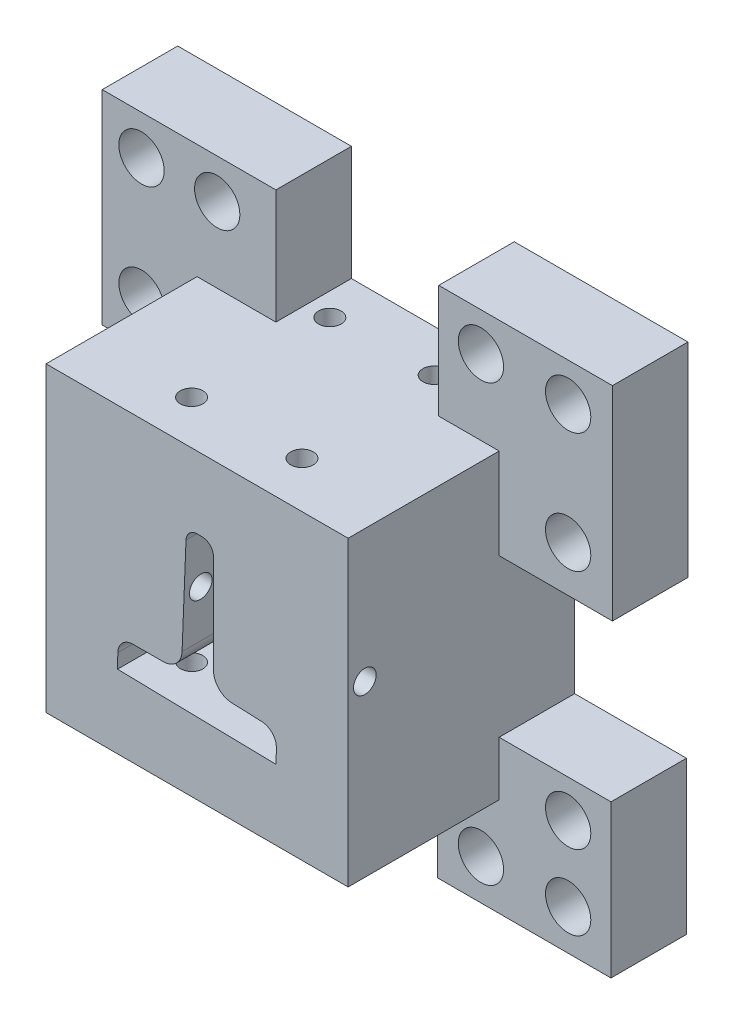
SolidWorks part; units mm, degrees
ref_plane "Plan de face" through (0, 0, 0) normal (0, 0, 1) x (1, 0, 0)
ref_plane "Plan de dessus" through (0, 0, 0) normal (0, 1, 0) x (1, 0, 0)
ref_plane "Plan de droite" through (0, 0, 0) normal (1, 0, 0) x (0, 0, -1)
sketch "Esquisse1" plane through (0, 0, 0) normal (0, 0, 1) x (1, 0, 0)
  line L0 (0, 699.6358) -> (0, -119.0526) construction
  line L1 (-20, 579.5765) -> (20, 579.5765)
  line L2 (-20, 579.5765) -> (-20, 539.5765)
  line L3 (-20, 539.5765) -> (20, 539.5765)
  line L4 (20, 579.5765) -> (20, 539.5765)
  line L5 (-10.0257, 549.7771) -> (9.9703, 549.3771) construction
  line L6 (9.9703, 549.3771) -> (9.9989, 550.8065) construction
  line L7 (8.5592, 552.3353) -> (4.552, 552.4957) construction
  line L8 (1.672, 555.4933) -> (1.672, 568.5669) construction
  line L9 (-0.9666, 568.6197) -> (-1.4895, 555.5565) construction
  line L10 (-4.4871, 552.6765) -> (-8.4974, 552.6765) construction
  line L11 (-10.0257, 549.7771) -> (-9.9971, 551.2065) construction
  line L12 (0.0526, 569.5795) -> (0.692, 569.5667) construction
  line L13 (-10.0257, 549.7771) -> (9.9703, 549.3771)
  line L14 (9.9703, 549.3771) -> (9.9989, 550.8065)
  line L15 (8.5592, 552.3353) -> (4.552, 552.4957)
  line L16 (1.672, 555.4933) -> (1.672, 568.5669)
  line L17 (-0.9666, 568.6197) -> (-1.4895, 555.5565)
  line L18 (-4.4871, 552.6765) -> (-8.4974, 552.6765)
  line L19 (-10.0257, 549.7771) -> (-9.9971, 551.2065)
  line L20 (0.0526, 569.5795) -> (0.692, 569.5667)
  arc A0 (9.9989, 550.8065) -> (8.5592, 552.3353) centre (8.4992, 550.8365) ccw construction
  arc A1 (1.672, 555.4933) -> (4.552, 552.4957) centre (4.672, 555.4933) ccw construction
  arc A2 (1.672, 568.5669) -> (0.692, 569.5667) centre (0.672, 568.5669) ccw construction
  arc A3 (0.0526, 569.5795) -> (-0.9666, 568.6197) centre (0.0326, 568.5797) ccw construction
  arc A4 (-4.4871, 552.6765) -> (-1.4895, 555.5565) centre (-4.4871, 555.6765) ccw construction
  arc A5 (-8.4974, 552.6765) -> (-9.9971, 551.2065) centre (-8.4974, 551.1765) ccw construction
  arc A6 (9.9989, 550.8065) -> (8.5592, 552.3353) centre (8.4992, 550.8365) ccw
  arc A7 (1.672, 555.4933) -> (4.552, 552.4957) centre (4.672, 555.4933) ccw
  arc A8 (1.672, 568.5669) -> (0.692, 569.5667) centre (0.672, 568.5669) ccw
  arc A9 (0.0526, 569.5795) -> (-0.9666, 568.6197) centre (0.0326, 568.5797) ccw
  arc A10 (-4.4871, 552.6765) -> (-1.4895, 555.5565) centre (-4.4871, 555.6765) ccw
  arc A11 (-8.4974, 552.6765) -> (-9.9971, 551.2065) centre (-8.4974, 551.1765) ccw
  dimension "D1" = 20
  dimension "D2" = 20
  dimension "D3" = 40
extrude "Boss.-Extru.1" add sketch "Esquisse1" along normal blind 30
sketch "Esquisse3" plane through (0, 0, 30) normal (0, 0, 1) x (1, 0, 0)
  line L16 (0.702, 570.0666) -> (0.0626, 570.0794)
  line L17 (-1.4662, 568.6397) -> (-1.9891, 555.5765)
  line L18 (-4.4871, 553.1765) -> (-8.4974, 553.1765)
  line L19 (-10.497, 551.2165) -> (-10.5356, 549.2872)
  line L20 (-10.5356, 549.2872) -> (10.4602, 548.8672)
  line L21 (10.4602, 548.8672) -> (10.4988, 550.7965)
  line L22 (8.5791, 552.8349) -> (4.572, 552.9953)
  line L23 (2.172, 555.4933) -> (2.172, 568.5669)
  line L24 (0.702, 570.0666) -> (0.0626, 570.0794)
  line L25 (-1.4662, 568.6397) -> (-1.9891, 555.5765)
  line L26 (-4.4871, 553.1765) -> (-8.4974, 553.1765)
  line L27 (-10.497, 551.2165) -> (-10.5356, 549.2872)
  line L28 (-10.5356, 549.2872) -> (10.4602, 548.8672)
  line L29 (10.4602, 548.8672) -> (10.4988, 550.7965)
  line L30 (8.5791, 552.8349) -> (4.572, 552.9953)
  line L31 (2.172, 555.4933) -> (2.172, 568.5669)
  arc A12 (2.172, 568.5669) -> (0.702, 570.0666) centre (0.672, 568.5669) ccw
  arc A13 (0.0626, 570.0794) -> (-1.4662, 568.6397) centre (0.0326, 568.5797) ccw
  arc A14 (-4.4871, 553.1765) -> (-1.9891, 555.5765) centre (-4.4871, 555.6765) ccw
  arc A15 (-8.4974, 553.1765) -> (-10.497, 551.2165) centre (-8.4974, 551.1765) ccw
  arc A16 (10.4988, 550.7965) -> (8.5791, 552.8349) centre (8.4992, 550.8365) ccw
  arc A17 (2.172, 555.4933) -> (4.572, 552.9953) centre (4.672, 555.4933) ccw
  arc A18 (2.172, 568.5669) -> (0.702, 570.0666) centre (0.672, 568.5669) ccw
  arc A19 (0.0626, 570.0794) -> (-1.4662, 568.6397) centre (0.0326, 568.5797) ccw
  arc A20 (-4.4871, 553.1765) -> (-1.9891, 555.5765) centre (-4.4871, 555.6765) ccw
  arc A21 (-8.4974, 553.1765) -> (-10.497, 551.2165) centre (-8.4974, 551.1765) ccw
  arc A22 (10.4988, 550.7965) -> (8.5791, 552.8349) centre (8.4992, 550.8365) ccw
  arc A23 (2.172, 555.4933) -> (4.572, 552.9953) centre (4.672, 555.4933) ccw
  dimension "D1" = 0.5
extrude "Enlèv. mat.-Extru.1" cut sketch "Esquisse3" against normal blind 30
sketch "Esquisse4" plane through (0, 539.5765, 0) normal (0, -1, 0) x (1, 0, 0)
  line L0 (0, -5.5078) -> (0.702, 27.3077) construction
  line L1 (0.702, 0) -> (0.702, 30) construction
  circle A0 centre (-6.5234, 24.2039) radius 1.5
  circle A1 centre (-6.5234, 5.9016) radius 1.5
  circle A2 centre (7.0054, 5.6122) radius 1.5
  circle A3 centre (7.788, 23.8977) radius 1.5
extrude "Enlèv. mat.-Extru.2" cut sketch "Esquisse4" against normal through all
sketch "Esquisse5" plane through (-20, 0, 0) normal (-1, 0, 0) x (0, 0, 1)
  circle A0 centre (27.7868, 562.0494) radius 1.5
  circle A1 centre (2.0009, 562.0494) radius 1.5
extrude "Enlèv. mat.-Extru.3" cut sketch "Esquisse5" against normal through all
sketch "Esquisse6" plane through (0, 0, 0) normal (0, 0, -1) x (-1, 0, 0)
  line L0 (-20, 539.5765) -> (-20, 579.5765) construction
  line L1 (-12, 567.5765) -> (-35, 567.5765)
  line L2 (-12, 567.5765) -> (-12, 594.5765)
  line L3 (-12, 594.5765) -> (-35, 594.5765)
  line L4 (-35, 567.5765) -> (-35, 594.5765)
  line L5 (-20, 579.5765) -> (20, 579.5765) construction
  line L6 (10.6661, 547.3898) -> (33.6661, 547.3898)
  line L7 (9.5636, 594.7416) -> (32.5636, 594.7416)
  line L8 (9.5636, 594.7416) -> (9.5636, 567.7416)
  line L9 (9.5636, 567.7416) -> (32.5636, 567.7416)
  line L10 (32.5636, 594.7416) -> (32.5636, 567.7416)
  line L11 (10.6661, 547.3898) -> (10.6661, 527.1835)
  line L12 (10.6661, 527.1835) -> (33.6661, 527.1835)
  line L13 (33.6661, 547.3898) -> (33.6661, 527.1835)
  line L14 (-34.806, 546.7515) -> (-11.806, 546.7515)
  line L15 (-34.806, 546.7515) -> (-34.806, 526.5452)
  line L16 (-34.806, 526.5452) -> (-11.806, 526.5452)
  line L17 (-11.806, 546.7515) -> (-11.806, 526.5452)
  dimension "D1" = 15
  dimension "D2" = 15
  dimension "D3" = 8
  dimension "D4" = 12
  dimension "D5" = 23
  dimension "D6" = 27
  dimension "D7" = 23
  dimension "D8" = 23
extrude "Boss.-Extru.2" add sketch "Esquisse6" against normal blind 10
sketch "Esquisse7" plane through (0, 0, 10) normal (0, 0, 1) x (1, 0, 0)
  circle A0 centre (-27.3597, 589.5163) radius 3
  circle A1 centre (-27.3597, 573.6648) radius 3
  circle A2 centre (-27.3597, 541.7732) radius 3
  circle A3 centre (-27.3597, 531.8831) radius 3
  circle A4 centre (-17.3384, 531.8831) radius 3
  circle A5 centre (-17.3384, 589.5163) radius 3
  circle A6 centre (17.5876, 589.5163) radius 3
  circle A7 centre (29.136, 589.5163) radius 3
  circle A8 centre (29.136, 573.6648) radius 3
  circle A9 centre (29.136, 541.7732) radius 3
  circle A10 centre (29.136, 531.8831) radius 3
  circle A11 centre (17.5876, 531.8831) radius 3
extrude "Enlèv. mat.-Extru.4" cut sketch "Esquisse7" against normal through all
